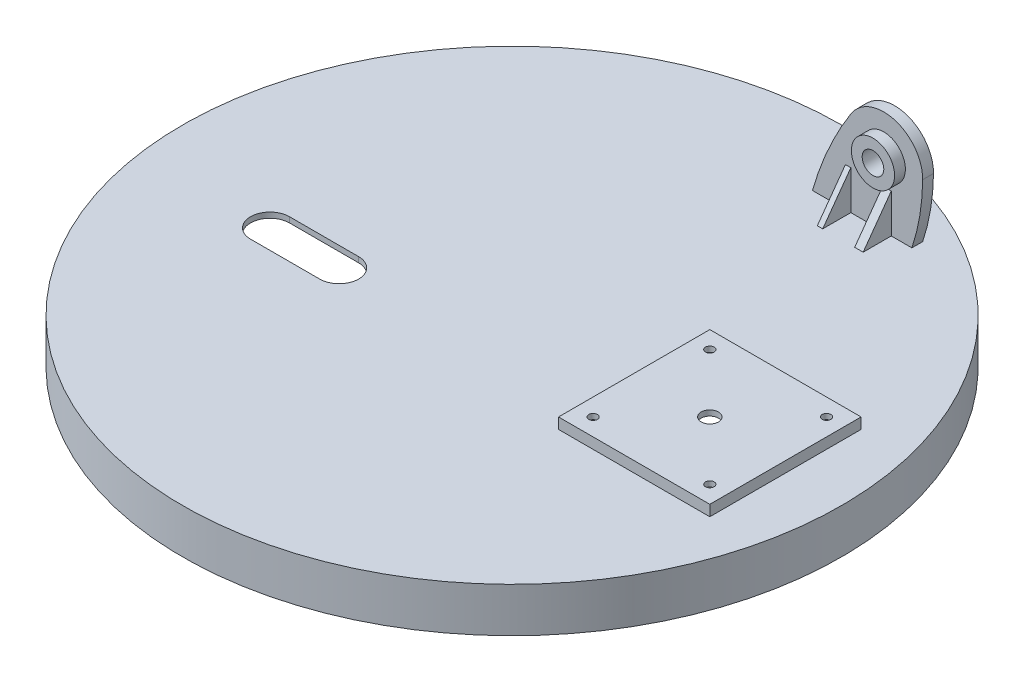
SolidWorks part; units mm, degrees
ref_plane "前视基准面" through (0, 0, 0) normal (0, 0, 1) x (1, 0, 0)
ref_plane "上视基准面" through (0, 0, 0) normal (0, 1, 0) x (1, 0, 0)
ref_plane "右视基准面" through (0, 0, 0) normal (1, 0, 0) x (0, 0, -1)
sketch "草图1" plane through (0, 0, 0) normal (0, 1, 0) x (1, 0, 0)
  circle A0 centre (0, 0) radius 305
  dimension "D1" = 610
extrude "凸台-拉伸1" add sketch "草图1" along normal blind 41.2
sketch "草图2" plane through (0, 41.2, 0) normal (0, 1, 0) x (1, 0, 0)
  line L1 (113, -70) -> (253, -70)
  line L2 (113, -70) -> (113, 70)
  line L3 (113, 70) -> (253, 70)
  line L4 (253, -70) -> (253, 70)
  line L5 (113, -70) -> (253, 70) construction
  line L6 (113, 70) -> (253, -70) construction
  line L7 (237, -54) -> (129, -54) construction
  line L8 (237, -54) -> (237, 54) construction
  line L9 (237, 54) -> (129, 54) construction
  line L10 (129, -54) -> (129, 54) construction
  line L11 (237, -54) -> (129, 54) construction
  line L12 (237, 54) -> (129, -54) construction
  point P0 (183, 0)
  point P5 (183, 0)
  dimension "D1" = 140
  dimension "D2" = 113
  dimension "D3" = 108
extrude "凸台-拉伸2" add sketch "草图2" along normal blind 10
shell "抽壳1" thickness 5
sketch "草图3" plane through (0, 41.2, 0) normal (0, 1, 0) x (1, 0, 0)
  line L0 (-182, -42) -> (-118, -42) construction
  line L1 (-182, -24) -> (-118, -24)
  line L2 (-182, -60) -> (-118, -60)
  arc A0 (-182, -24) -> (-182, -60) centre (-182, -42) ccw
  arc A1 (-118, -60) -> (-118, -24) centre (-118, -42) ccw
  point P2 (-150, -42)
  point P7 (-200, -42)
  point P8 (-100, -42)
  dimension "D4" = 100
  dimension "D1" = 100
  dimension "D2" = 36
  dimension "D3" = 42
extrude "切除-拉伸1" cut sketch "草图3" against normal through all
sketch "草图4" plane through (0, 41.2, 0) normal (0, 1, 0) x (1, 0, 0)
  line L1 (39, 249) -> (159, 249)
  line L2 (39, 249) -> (39, 239)
  line L3 (39, 239) -> (159, 239)
  line L4 (159, 249) -> (159, 239)
  line L5 (39, 249) -> (159, 239) construction
  line L6 (39, 239) -> (159, 249) construction
  point P0 (99, 244)
  dimension "D1" = 39
  dimension "D2" = 249
  dimension "D3" = 10
  dimension "D4" = 120
extrude "凸台-拉伸3" add sketch "草图4" along normal blind 150
sketch "草图5" plane through (0, 0, -239) normal (0, 0, 1) x (1, 0, 0)
  line L1 (39, 191.2) -> (39, 41.2) construction
  line L2 (39, 41.2) -> (159, 41.2) construction
  line L3 (305, 41.2) -> (-305, 41.2) construction
  line L4 (39, 41.2) -> (131, 41.2)
  line L5 (159, 41.2) -> (131, 41.2)
  line L9 (39, 41.2) -> (159, 41.2)
  line L10 (159, 41.2) -> (159, 191.2)
  line L11 (159, 191.2) -> (39, 191.2)
  line L12 (39, 191.2) -> (39, 41.2)
  line L13 (39, 41.2) -> (159, 41.2)
  line L14 (159, 41.2) -> (159, 191.2)
  line L15 (159, 191.2) -> (39, 191.2)
  line L16 (39, 191.2) -> (39, 41.2)
  arc A0 (39, 41.2) -> (74.6468, 120.5567) centre (327.5902, -40.7493) cw
  arc A1 (74.6468, 120.5567) -> (140.998, 100.8218) centre (105, 101.2) cw
  arc A2 (140.998, 100.8218) -> (131, 41.2) centre (-53.9912, 102.8705) cw
  line M5 (39, 41.2) -> (159, 41.2)
  line M6 (159, 41.2) -> (159, 191.2)
  line M7 (159, 191.2) -> (39, 191.2)
  line M8 (39, 191.2) -> (39, 41.2)
  dimension "D2" = 300
  dimension "D3" = 36
  dimension "D4" = 195
  dimension "D1" = 105
  dimension "D5" = 92
  dimension "D6" = 60
  dimension "D7" = 0
extrude "切除-拉伸3" cut sketch "草图5" against normal blind 150 contours A1 A2 A0 M5 M6 M7 M8
sketch "草图6" plane through (0, 0, -239) normal (0, 0, 1) x (1, 0, 0)
  circle A0 centre (105, 101.2) radius 10
  dimension "D1" = 20
extrude "切除-拉伸4" cut sketch "草图6" against normal blind 150
sketch "草图7" plane through (0, 0, -239) normal (0, 0, 1) x (1, 0, 0)
  circle A0 centre (105, 101.2) radius 20
  circle A1 centre (105, 101.2) radius 10 construction
  circle A2 centre (105, 101.2) radius 10
  dimension "D1" = 40
extrude "凸台-拉伸4" add sketch "草图7" along normal blind 10
sketch "草图8" plane through (0, 0, -239) normal (0, 0, 1) x (1, 0, 0)
  line L0 (39, 41.2) -> (131, 41.2) construction
  line L1 (69.5, 41.2) -> (74.5, 41.2)
  line L2 (69.5, 41.2) -> (69.5, 77.2)
  line L3 (69.5, 77.2) -> (74.5, 77.2)
  line L4 (74.5, 41.2) -> (74.5, 77.2)
  line L6 (104.0806, 41.2) -> (111.9194, 41.2)
  line L7 (104.0806, 41.2) -> (104.0806, 77.2)
  line L8 (104.0806, 77.2) -> (111.9194, 77.2)
  line L9 (111.9194, 41.2) -> (111.9194, 77.2)
  point P10 (72, 41.2)
  point P12 (108, 41.2)
  dimension "D1" = 72
  dimension "D2" = 36
  dimension "D3" = 5
  dimension "D4" = 36
extrude "凸台-拉伸5" add sketch "草图8" along normal blind 26
sketch "草图10" plane through (111.9194, 0, 0) normal (1, 0, 0) x (0, 0, -1)
  line L0 (213, 41.2) -> (239, 77.2)
  line L1 (239, 77.2) -> (213, 77.2)
  line L2 (213, 77.2) -> (213, 41.2)
extrude "切除-拉伸5" cut sketch "草图10" against normal through all
sketch "草图11" plane through (0, 0, 0) normal (0, 0, 1) x (1, 0, 0)
  line L1 (0, 0) -> (0, 93.9077) construction
  line L2 (-75, 36.2) -> (-75, 31.2)
  line L3 (-75, 31.2) -> (-56, 31.2)
  line L4 (-56, 31.2) -> (-56, 36.2)
  line L5 (-56, 36.2) -> (-75, 36.2)
  line L6 (-85, 36.2) -> (-80, 36.2)
  line L7 (-80, 36.2) -> (-80, -10.3)
  line L8 (-80, -10.3) -> (-85, -10.3)
  line L9 (-85, -10.3) -> (-85, 36.2)
  line L10 (305, 41.2) -> (-305, 41.2) construction
  dimension "D1" = 5
  dimension "D2" = 150
  dimension "D3" = 170
  dimension "D4" = 19
  dimension "D5" = 5
  dimension "D6" = 5
  dimension "D7" = 51.5
revolve "旋转1" add sketch "草图11" angle 360 about L1
sketch "草图18" plane through (0, 51.2, 0) normal (0, 1, 0) x (1, 0, 0)
  line L0 (113, 70) -> (253, -70) construction
  line L1 (253, 70) -> (113, -70) construction
  line L3 (237, -54) -> (129, -54) construction
  line L4 (237, -54) -> (237, 54) construction
  line L5 (237, 54) -> (129, 54) construction
  line L6 (129, -54) -> (129, 54) construction
  line L7 (237, -54) -> (129, 54) construction
  line L8 (237, 54) -> (129, -54) construction
  circle A0 centre (237, 54) radius 4
  circle A1 centre (237, -54) radius 4
  circle A2 centre (129, -54) radius 4
  circle A3 centre (129, 54) radius 4
  circle A4 centre (183, 0) radius 8
  point P8 (183, 0)
  dimension "D2" = 8
  dimension "D3" = 16
  dimension "D1" = 108
extrude "切除-拉伸9" cut sketch "草图18" against normal through all
